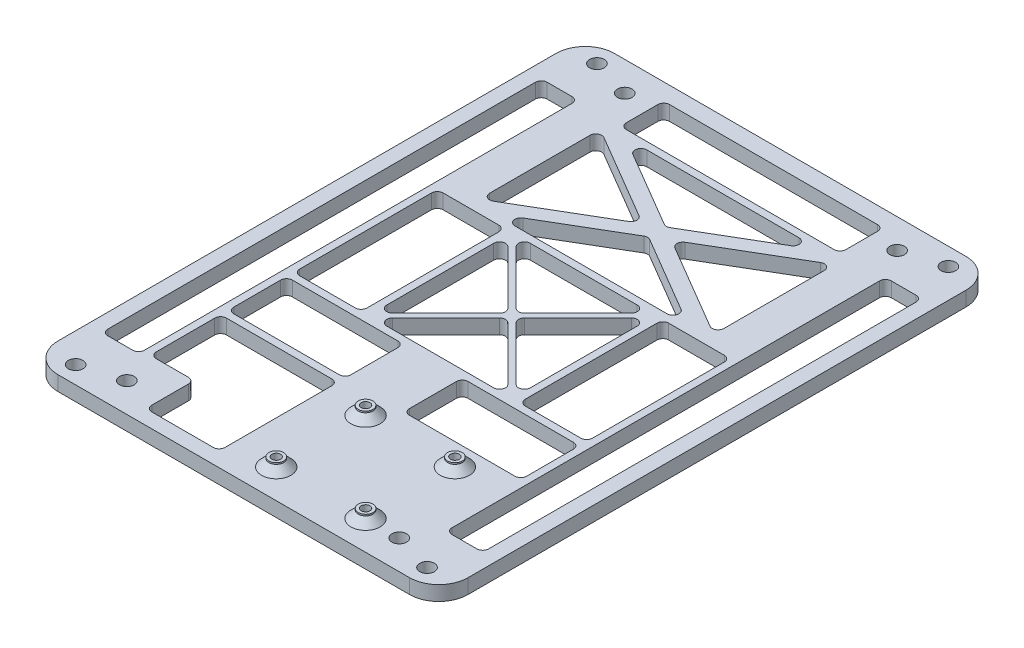
SolidWorks part; units mm, degrees
ref_plane "Front Plane" through (0, 0, 0) normal (0, 0, 1) x (1, 0, 0)
ref_plane "Top Plane" through (0, 0, 0) normal (0, 1, 0) x (1, 0, 0)
ref_plane "Right Plane" through (0, 0, 0) normal (1, 0, 0) x (0, 0, -1)
sketch "Sketch1" plane through (0, 0, 0) normal (0, 1, 0) x (1, 0, 0)
  line L0 (-70, -95) -> (70, -95)
  line L1 (-70, -95) -> (-70, 95)
  line L2 (-70, 95) -> (70, 95)
  line L3 (70, -95) -> (70, 95)
  line L4 (-70, -95) -> (70, 95) construction
  line L5 (-70, 95) -> (70, -95) construction
  line L6 (0, 0) -> (0, 29.3222) construction
  line L7 (0, 29.3222) -> (0, 0) construction
  line L8 (0, 0) -> (23.2574, 0) construction
  circle A0 centre (-60, 89) radius 2.5
  circle A1 centre (60, 89) radius 2.5
  circle A2 centre (-60, -89) radius 2.5
  circle A3 centre (60, -89) radius 2.5
  circle A4 centre (60, -89) radius 2.5
  circle A5 centre (-60, -89) radius 2.5
  point P0 (0, 0)
  point P5 (0, 0)
  dimension "D3" = 5
  dimension "D6" = 120
  dimension "D1" = 190
  dimension "D2" = 140
  dimension "D4" = 6
  dimension "D5" = 10
extrude "Boss-Extrude1" add sketch "Sketch1" along normal blind 5 contours L0 L3 L2 L1 A3 A1 A0 A2
fillet "Fillet1" radius 10 4 edges at (-70, 2.5, -95) (70, 2.5, -95) (70, 2.5, 95) (-70, 2.5, 95)
sketch "Sketch2" plane through (0, 5, 0) normal (0, 1, 0) x (1, 0, 0)
  line L0 (-39, -37.5) -> (-39, -86.5) construction
  line L1 (-39, -37.5) -> (39, -37.5) construction
  line L2 (-39, -34) -> (39, -34) construction
  line L3 (42.5, -62) -> (-39, -62) construction
  line L4 (-42.5, -37.5) -> (-42.5, -86.5) construction
  line L5 (42.5, -37.5) -> (42.5, -86.5) construction
  line L6 (-39, -90) -> (39, -90) construction
  line L7 (-60, -95) -> (60, -95) construction
  line L8 (0, -34) -> (0, -26.5247) construction
  circle A1 centre (39, -37.5) radius 1.5
  circle A2 centre (39, -86.5) radius 1.5
  arc A4 (-39, -34) -> (-42.5, -37.5) centre (-39, -37.5) ccw construction
  arc A5 (-39, -90) -> (-42.5, -86.5) centre (-39, -86.5) cw construction
  arc A6 (42.5, -37.5) -> (39, -34) centre (39, -37.5) ccw construction
  arc A7 (42.5, -86.5) -> (39, -90) centre (39, -86.5) cw construction
  circle A8 centre (-19, -37.5) radius 1.5
  circle A9 centre (-19, -86.5) radius 1.5
  point P15 (1.75, -62)
  dimension "D1" = 3
  dimension "D2" = 58
  dimension "D3" = 49
  dimension "D4" = 85
  dimension "D5" = 56
  dimension "D6" = 5
sketch "Sketch3" plane through (0, 5, 0) normal (0, 1, 0) x (1, 0, 0)
  line L0 (4.5, -54.5) -> (35, -85) construction
  line L1 (4.5, -85) -> (35, -54.5) construction
  line L2 (-0.9781, -0.9539) -> (-0.9659, -0.967) construction
  line L4 (-60, -95) -> (60, -95) construction
  line L5 (70, -85) -> (70, 85) construction
  line L7 (4.5, -85) -> (35, -85) construction
  line L8 (4.5, -85) -> (4.5, -54.5) construction
  line L9 (4.5, -54.5) -> (35, -54.5) construction
  line L10 (35, -85) -> (35, -54.5) construction
  circle A0 centre (4.5, -54.5) radius 1.5
  circle A1 centre (35, -54.5) radius 1.5
  circle A3 centre (4.5, -85) radius 1.5
  circle A4 centre (35, -85) radius 1.5
  point P0 (19.75, -69.75)
  point P12 (19.75, -69.75)
  dimension "D3" = 3
  dimension "D4" = 35
  dimension "D1" = 10
  dimension "D2" = 30.5
extrude "Cut-Extrude2" cut sketch "Sketch3" against normal blind 10
sketch "Sketch7" plane through (0, 5, 0) normal (0, 1, 0) x (1, 0, 0)
  line L0 (-60, 95) -> (60, 95) construction
  line L1 (11.375, 75.8) -> (-11.375, 75.8)
  line L2 (11.375, 75.8) -> (11.375, 88)
  line L3 (11.375, 88) -> (-11.375, 88)
  line L4 (-11.375, 75.8) -> (-11.375, 88)
  line L5 (11.375, 75.8) -> (-11.375, 88) construction
  line L6 (11.375, 88) -> (-11.375, 75.8) construction
  point P0 (0, 81.9)
  dimension "D1" = 22.75
  dimension "D2" = 12.2
  dimension "D3" = 7
sketch "Sketch14" plane through (0, 5, 0) normal (0, 1, 0) x (1, 0, 0)
  line L0 (0, 0) -> (115.2756, 0) construction
  line L1 (-65, 75) -> (-52.5, 75)
  line L2 (-65, 75) -> (-65, -75)
  line L3 (-65, -75) -> (-52.5, -75)
  line L4 (-52.5, 75) -> (-52.5, -75)
  line L9 (-65, 0) -> (-110.3251, 0) construction
  line L10 (0, -85) -> (0, -54.5) construction
  line L11 (65, -75) -> (52.5, -75)
  line L12 (52.5, 75) -> (52.5, -75)
  line L13 (65, 75) -> (65, -75)
  line L14 (65, 75) -> (52.5, 75)
  line L15 (-70, -85) -> (-70, 85) construction
  line L16 (4.5, -54.5) -> (35, -54.5) construction
  line L17 (-35, -49.5) -> (-10, -49.5)
  line L18 (-35, -73.5) -> (-35, -90)
  line L19 (-35, -90) -> (-10, -90)
  line L20 (-10, -49.5) -> (-10, -90)
  line L21 (4.5, -85) -> (35, -85) construction
  line L22 (-60, -95) -> (60, -95) construction
  line L23 (-60, 95) -> (60, 95) construction
  line L24 (-35.5, 89.3) -> (35.5, 89.3)
  line L25 (-37.5, 87.3) -> (-37.5, 76.5)
  line L26 (-35.5, 74.5) -> (35.5, 74.5)
  line L27 (37.5, 87.3) -> (37.5, 76.5)
  line L28 (-37.5, 89.3) -> (37.5, 74.5) construction
  line L29 (-37.5, 74.5) -> (37.5, 89.3) construction
  line L30 (-24.5, -23.0858) -> (-1.4142, 0)
  line L31 (-35, -49.5) -> (-50, -49.5)
  line L33 (-35, -73.5) -> (-50, -73.5)
  line L34 (-50, -49.5) -> (-50, -73.5)
  line L35 (-25, -25) -> (25, -25) construction
  line L36 (-25, -25) -> (-25, 25) construction
  line L37 (-25, 25) -> (25, 25) construction
  line L38 (25, -25) -> (25, 25) construction
  line L39 (-25, -25) -> (25, 25) construction
  line L40 (-25, 25) -> (25, -25) construction
  line L41 (-1.4142, 0) -> (-24.5, 23.0858)
  line L42 (-24.5, 23.0858) -> (-24.5, -23.0858)
  line L43 (23.0858, 24.5) -> (-23.0858, 24.5)
  line L44 (-23.0858, 24.5) -> (0, 1.4142)
  line L45 (0, 1.4142) -> (23.0858, 24.5)
  line L46 (24.5, -23.0858) -> (24.5, 23.0858)
  line L47 (24.5, 23.0858) -> (1.4142, 0)
  line L48 (1.4142, 0) -> (24.5, -23.0858)
  line L49 (-23.0858, -24.5) -> (23.0858, -24.5)
  line L50 (23.0858, -24.5) -> (0, -1.4142)
  line L51 (0, -1.4142) -> (-23.0858, -24.5)
  arc A1 (-37.5, 76.5) -> (-35.5, 74.5) centre (-35.5, 76.5) ccw
  arc A2 (35.5, 74.5) -> (37.5, 76.5) centre (35.5, 76.5) ccw
  arc A3 (37.5, 87.3) -> (35.5, 89.3) centre (35.5, 87.3) ccw
  arc A4 (-35.5, 89.3) -> (-37.5, 87.3) centre (-35.5, 87.3) ccw
  point P31 (-10, -69.75)
  point P32 (0, -69.75)
  point P35 (0, 81.9)
  point P75 (0, 0)
  dimension "D9" = 2
  dimension "D1" = 12.5
  dimension "D2" = 150
  dimension "D3" = 5
  dimension "D4" = 25
  dimension "D5" = 5
  dimension "D6" = 10
  dimension "D7" = 5.7
  dimension "D8" = 75
  dimension "D10" = 16.5
  dimension "D11" = 2.5
  dimension "D12" = 50
  dimension "D13" = 1
  dimension "D14" = 1
  dimension "D15" = 1
  dimension "D16" = 4
extrude "Cut-Extrude9" cut sketch "Sketch14" against normal blind 10
fillet "Fillet3" radius 2 26 edges at (65, 2.5, 75) (52.5, 2.5, 75) (52.5, 2.5, -75) (65, 2.5, -75) (-52.5, 2.5, -75) (-65, 2.5, -75) (-65, 2.5, 75) (-52.5, 2.5, 75) (-35, 2.5, 90) (-10, 2.5, 90) (-10, 2.5, 49.5) (-50, 2.5, 73.5) (-50, 2.5, 49.5) (-35, 2.5, 73.5) (23.0858, 2.5, -24.5) (24.5, 2.5, -23.0858) (0, 2.5, -1.4142) (-23.0858, 2.5, -24.5) (1.4142, 2.5, 0) (24.5, 2.5, 23.0858) (23.0858, 2.5, 24.5) (0, 2.5, 1.4142) (-23.0858, 2.5, 24.5) (-24.5, 2.5, 23.0858) (-1.4142, 2.5, 0) (-24.5, 2.5, -23.0858)
sketch "Sketch17" plane through (0, 5, 0) normal (0, 1, 0) x (1, 0, 0)
  line L0 (0, 0) -> (0, 62.5659) construction
  line L2 (52.5, 73) -> (52.5, -73) construction
  line L4 (46.5, 85) -> (46.5, -85) construction
  line L7 (46.5, 0) -> (37.6627, 0) construction
  line L8 (65, 0) -> (83.731, 0) construction
  line L9 (65, -73) -> (65, 73) construction
  circle A0 centre (46.5, 85) radius 2.5
  circle A1 centre (46.5, -85) radius 2.5
  circle A2 centre (-46.5, -85) radius 2.5
  circle A3 centre (-46.5, 85) radius 2.5
  dimension "D1" = 5
  dimension "D4" = 6
  dimension "D3" = 6
  dimension "D5" = 170
extrude "Cut-Extrude12" cut sketch "Sketch17" against normal blind 10
sketch "Sketch18" plane through (0, 5, 0) normal (0, 1, 0) x (1, 0, 0)
  circle A0 centre (4.5, -54.5) radius 2.5
  circle A1 centre (4.5, -54.5) radius 1.5
  circle A2 centre (35, -54.5) radius 1.5
  circle A3 centre (35, -54.5) radius 2.5
  circle A4 centre (35, -85) radius 1.5
  circle A5 centre (35, -85) radius 2.5
  circle A6 centre (4.5, -85) radius 2.5
  circle A7 centre (4.5, -85) radius 1.5
  circle A8 centre (4.5, -85) radius 1.5 construction
  dimension "D1" = 5
extrude "Boss-Extrude2" add sketch "Sketch18" along normal blind 3
sketch "Sketch19" plane through (0, 5, 0) normal (0, 1, 0) x (1, 0, 0)
  line L0 (-18.2574, -24.5) -> (18.2574, -24.5) construction
  line L1 (-48, -47) -> (-12, -47)
  line L2 (-50, -45) -> (-50, -29)
  line L3 (-48, -27) -> (-12, -27)
  line L4 (50, -45) -> (50, -29)
  line L5 (-50, -47) -> (50, -27) construction
  line L6 (-50, -27) -> (50, -47) construction
  line L7 (-12, -49.5) -> (-48, -49.5) construction
  line L8 (-52.5, -73) -> (-52.5, 73) construction
  line L9 (52.5, 73) -> (52.5, -73) construction
  line L10 (0, -24.5) -> (0, 24.5) construction
  line L11 (-48, -24.5) -> (-29, -24.5)
  line L12 (-50, -22.5) -> (-50, 22.5)
  line L13 (-48, 24.5) -> (-29, 24.5)
  line L14 (-27, -22.5) -> (-27, 22.5)
  line L15 (-50, -24.5) -> (-27, 24.5) construction
  line L16 (-50, 24.5) -> (-27, -24.5) construction
  line L17 (18.2574, 24.5) -> (-18.2574, 24.5) construction
  line L18 (-24.5, 18.2574) -> (-24.5, -18.2574) construction
  line L19 (48, 24.5) -> (29, 24.5)
  line L20 (27, -22.5) -> (27, 22.5)
  line L21 (48, -24.5) -> (29, -24.5)
  line L22 (50, -22.5) -> (50, 22.5)
  line L23 (12, -27) -> (48, -27)
  line L25 (-10, -45) -> (-10, -29)
  line L27 (10, -45) -> (10, -29)
  line L28 (-10, -47) -> (10, -27) construction
  line L29 (-10, -27) -> (10, -47) construction
  line L30 (12, -47) -> (48, -47)
  line L31 (-10, -88) -> (-10, -51.5) construction
  line L32 (-50, -51.5) -> (-50, -71.5) construction
  line L33 (-35.5, 74.5) -> (35.5, 74.5) construction
  line L34 (-42.5, 24.5) -> (42.5, 24.5) construction
  line L35 (-42.5, 24.5) -> (-42.5, 74.5) construction
  line L36 (-42.5, 74.5) -> (42.5, 74.5) construction
  line L37 (42.5, 24.5) -> (42.5, 74.5) construction
  line L38 (-42.5, 24.5) -> (42.5, 74.5) construction
  line L39 (-42.5, 74.5) -> (42.5, 24.5) construction
  line L40 (-40, 66.6321) -> (-40, 32.3679)
  line L41 (-36.986, 30.644) -> (-7.8613, 47.7761)
  line L42 (-7.8613, 51.2239) -> (-36.986, 68.356)
  line L43 (-26.9887, 68.2761) -> (-1.014, 52.9969)
  line L44 (1.014, 52.9969) -> (26.9887, 68.2761)
  line L45 (25.9746, 72) -> (-25.9746, 72)
  line L46 (36.986, 30.644) -> (7.8613, 47.7761)
  line L47 (0, 49.5) -> (42.5, 49.5) construction
  line L48 (40, 66.6321) -> (40, 32.3679)
  line L49 (7.8613, 51.2239) -> (36.986, 68.356)
  line L50 (1.014, 46.0031) -> (26.9887, 30.7239)
  line L51 (-26.9887, 30.7239) -> (-1.014, 46.0031)
  line L52 (25.9746, 27) -> (-25.9746, 27)
  arc A0 (-50, -45) -> (-48, -47) centre (-48, -45) ccw
  arc A1 (48, -47) -> (50, -45) centre (48, -45) ccw
  arc A2 (50, -29) -> (48, -27) centre (48, -29) ccw
  arc A3 (-48, -27) -> (-50, -29) centre (-48, -29) ccw
  arc A4 (-27, -22.5) -> (-29, -24.5) centre (-29, -22.5) cw
  arc A5 (-48, -24.5) -> (-50, -22.5) centre (-48, -22.5) cw
  arc A6 (-48, 24.5) -> (-50, 22.5) centre (-48, 22.5) ccw
  arc A7 (-27, 22.5) -> (-29, 24.5) centre (-29, 22.5) ccw
  arc A8 (27, 22.5) -> (29, 24.5) centre (29, 22.5) cw
  arc A9 (27, -22.5) -> (29, -24.5) centre (29, -22.5) ccw
  arc A10 (48, -24.5) -> (50, -22.5) centre (48, -22.5) ccw
  arc A11 (48, 24.5) -> (50, 22.5) centre (48, 22.5) cw
  arc A12 (12, -47) -> (10, -45) centre (12, -45) cw
  arc A13 (12, -27) -> (10, -29) centre (12, -29) ccw
  arc A14 (-12, -47) -> (-10, -45) centre (-12, -45) ccw
  arc A15 (-10, -29) -> (-12, -27) centre (-12, -29) ccw
  arc A16 (-1.014, 52.9969) -> (1.014, 52.9969) centre (0, 54.7208) ccw
  arc A17 (26.9887, 68.2761) -> (25.9746, 72) centre (25.9746, 70) ccw
  arc A18 (-25.9746, 72) -> (-26.9887, 68.2761) centre (-25.9746, 70) ccw
  arc A19 (-40, 32.3679) -> (-36.986, 30.644) centre (-38, 32.3679) ccw
  arc A20 (-7.8613, 47.7761) -> (-7.8613, 51.2239) centre (-8.8754, 49.5) ccw
  arc A21 (-36.986, 68.356) -> (-40, 66.6321) centre (-38, 66.6321) ccw
  arc A22 (40, 32.3679) -> (36.986, 30.644) centre (38, 32.3679) cw
  arc A23 (7.8613, 47.7761) -> (7.8613, 51.2239) centre (8.8754, 49.5) cw
  arc A24 (36.986, 68.356) -> (40, 66.6321) centre (38, 66.6321) cw
  arc A25 (-1.014, 46.0031) -> (1.014, 46.0031) centre (0, 44.2792) cw
  arc A26 (26.9887, 30.7239) -> (25.9746, 27) centre (25.9746, 29) cw
  arc A27 (-25.9746, 27) -> (-26.9887, 30.7239) centre (-25.9746, 29) cw
  point P0 (0, -37)
  point P25 (-38.5, 0)
  point P36 (0, 0)
  point P64 (0, -37)
  point P83 (0, 49.5)
  dimension "D5" = 2
  dimension "D8" = 2
  dimension "D9" = 2.5
  dimension "D10" = 2
  dimension "D16" = 2
  dimension "D1" = 2.5
  dimension "D2" = 2.5
  dimension "D3" = 10
  dimension "D4" = 2.5
  dimension "D6" = 2.5
  dimension "D7" = 2.5
  dimension "D11" = 2.5
  dimension "D12" = 5
  dimension "D13" = 5
  dimension "D14" = 2.5
  dimension "D15" = 2.5
extrude "Cut-Extrude13" cut sketch "Sketch19" against normal through all
chamfer "Chamfer1" distance 2.5 angle 45 4 edges at (35, 5, 57) (4.5, 5, 57) (35, 5, 87.5) (4.5, 5, 87.5)
